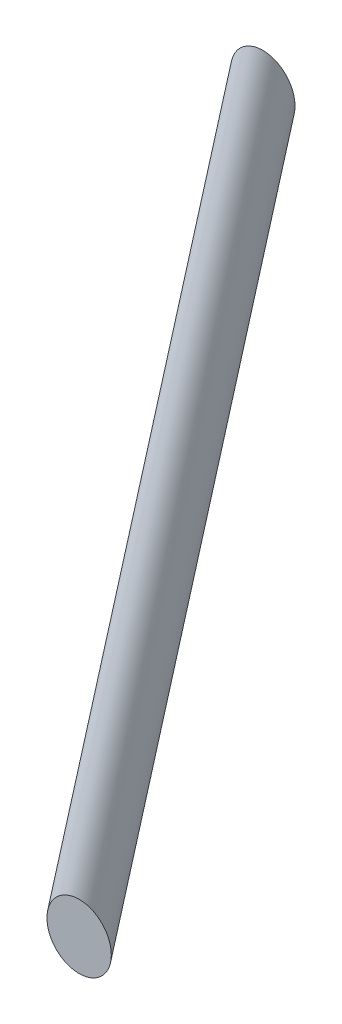
SolidWorks part; units mm, degrees
ref_plane "Front Plane" through (0, 0, 0) normal (0, 0, 1) x (1, 0, 0)
ref_plane "Top Plane" through (0, 0, 0) normal (0, 1, 0) x (1, 0, 0)
ref_plane "Right Plane" through (0, 0, 0) normal (1, 0, 0) x (0, 0, -1)
ref_plane "Plane1" through (110.4182, -191.25, 0) normal (-0.5, 0.866, 0) x (0.866, 0.5, 0)
sketch "Sketch2" plane through (110.4182, -191.25, 0) normal (-0.5, 0.866, 0) x (0.866, 0.5, 0)
  line L0 (-127.5, -230.5024) -> (-365, 0)
  line L1 (-70.5068, -230.5024) -> (-184.4932, -230.5024) construction
  line L2 (-347.5, 0) -> (-382.5, 0) construction
sketch "Sketch3" plane through (0, 0, 0) normal (0, 0, 1) x (1, 0, 0)
  circle A0 centre (-205.681, -373.75) radius 4.3491
sweep "Sweep1" add profiles "Sketch3" path "Sketch2"
